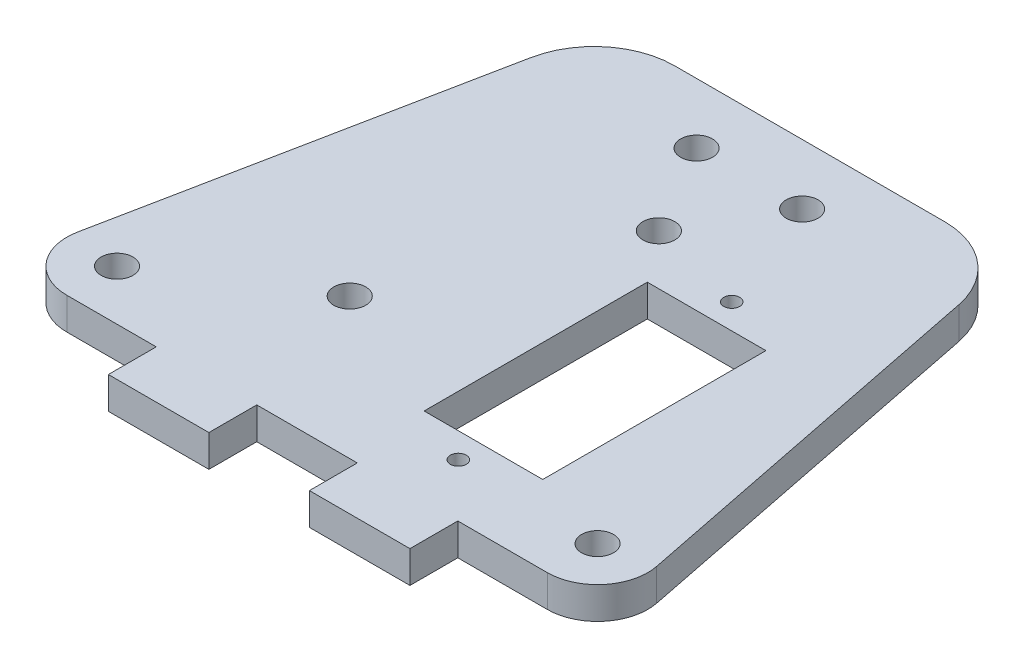
SolidWorks part; units mm, degrees
ref_plane "Alzado" through (0, 0, 0) normal (0, 0, 1) x (1, 0, 0)
ref_plane "Planta" through (0, 0, 0) normal (0, 1, 0) x (1, 0, 0)
ref_plane "Vista lateral" through (0, 0, 0) normal (1, 0, 0) x (0, 0, -1)
sketch "Croquis1" plane through (0, 0, 0) normal (0, 1, 0) x (1, 0, 0)
  line L0 (8.7138, 43.5689) -> (0, 0)
  line L1 (16.5584, 50) -> (43.4416, 50)
  line L3 (0, 0) -> (60, 0)
  line L5 (51.2862, 43.5689) -> (60, 0)
  line L6 (33.85, 7.8) -> (45.65, 2.8) construction
  line L7 (33.85, 30) -> (45.65, 30)
  line L9 (33.85, 30) -> (33.85, 7.8)
  line L10 (33.85, 7.8) -> (45.65, 7.8) construction
  line L11 (30, -1000) -> (30, 49000) construction
  line L12 (45.65, 30) -> (45.65, 7.8)
  line L13 (33.85, 30) -> (45.65, 30) construction
  line L14 (33.85, 30) -> (33.85, 35) construction
  line L15 (33.85, 35) -> (45.65, 35) construction
  line L16 (45.65, 30) -> (45.65, 35) construction
  line L17 (45.65, 7.8) -> (33.85, 7.8)
  line L18 (45.65, 7.8) -> (45.65, 2.8) construction
  line L19 (45.65, 2.8) -> (33.85, 2.8) construction
  line L20 (33.85, 7.8) -> (33.85, 2.8) construction
  line L21 (45.65, 2.8) -> (45.65, 35) construction
  line L22 (45.65, 35) -> (33.85, 30) construction
  line L23 (33.85, 35) -> (45.65, 30) construction
  line L24 (33.85, 2.8) -> (45.65, 7.8) construction
  circle A0 centre (20.25, 14) radius 9.5 construction
  circle A1 centre (39.75, 14) radius 9.5 construction
  circle A2 centre (20.25, 14) radius 12.5 construction
  circle A3 centre (39.75, 14) radius 12.5 construction
  circle A4 centre (39.75, 5.3) radius 0.7937
  circle A5 centre (39.75, 32.5) radius 0.7937
  circle A6 centre (20.25, 14) radius 1.5875
  circle A7 centre (24.75, 44) radius 1.5875
  circle A8 centre (35.25, 44) radius 1.5875
  circle A9 centre (24.75, 44) radius 4.7625 construction
  circle A10 centre (35.25, 44) radius 4.7625 construction
  arc A11 (51.2862, 43.5689) -> (43.4416, 50) centre (43.4416, 42) ccw
  arc A12 (8.7138, 43.5689) -> (16.5584, 50) centre (16.5584, 42) cw
  point P7 (50, 50)
  point P15 (30, 0)
  point P38 (10, 50)
  dimension "D6" = 19
  dimension "D7" = 19
  dimension "D5" = 25
  dimension "D10" = 25
  dimension "D18" = 1.5875
  dimension "D19" = 1.5875
  dimension "D20" = 3.175
  dimension "D21" = 3.175
  dimension "D22" = 3.175
  dimension "D26" = 9.525
  dimension "D27" = 9.525
  dimension "D29" = 8
  dimension "D1" = 60
  dimension "D3" = 40
  dimension "D4" = 20
  dimension "D8" = 19.5
  dimension "D9" = 14
  dimension "D11" = 9.75
  dimension "D12" = 22.2
  dimension "D13" = 11.8
  dimension "D14" = 5
  dimension "D15" = 5.9
  dimension "D16" = 5
  dimension "D17" = 7.8
  dimension "D23" = 4.5
  dimension "D24" = 4.5
  dimension "D25" = 30
  dimension "D28" = 50
extrude "Saliente-Extruir1" add sketch "Croquis1" along normal blind 3.175
sketch "Croquis2" plane through (0, 3.175, 0) normal (0, 1, 0) x (1, 0, 0)
  line L0 (0, 0) -> (60, 0) construction
  line L2 (60, 0) -> (51.2862, 43.5689) construction
  line L3 (53.901, 0) -> (60, 0)
  line L7 (43.4416, 50) -> (16.5584, 50)
  line L8 (8.7138, 43.5689) -> (0, 0)
  line L9 (0, 0) -> (60, 0)
  line L10 (60, 0) -> (51.2862, 43.5689)
  line L12 (1.1961, 5.9806) -> (0, 0)
  line L13 (0, 0) -> (6.099, 0)
  line L14 (60, 0) -> (58.8039, 5.9806)
  circle A0 centre (30, 35) radius 1.5875
  circle A1 centre (6.099, 5) radius 1.5875
  circle A2 centre (53.901, 5) radius 1.5875
  circle A3 centre (24.75, 44) radius 4.7625 construction
  circle A4 centre (35.25, 44) radius 4.7625 construction
  arc A6 (53.901, 0) -> (58.8039, 5.9806) centre (53.901, 5) ccw
  arc A7 (1.1961, 5.9806) -> (6.099, 0) centre (6.099, 5) ccw
  arc A9 (51.2862, 43.5689) -> (43.4416, 50) centre (43.4416, 42) ccw
  arc A10 (16.5584, 50) -> (8.7138, 43.5689) centre (16.5584, 42) ccw
  dimension "D1" = 9.525
  dimension "D2" = 9.525
  dimension "D3" = 3.175
  dimension "D4" = 3.175
  dimension "D5" = 3.175
  dimension "D6" = 5
  dimension "D7" = 10
  dimension "D9" = 5
  dimension "D10" = 30
  dimension "D11" = 35
  dimension "D8" = 0
extrude "Cortar-Extruir1" cut sketch "Croquis2" against normal blind 3.175
sketch "Croquis3" plane through (0, 3.175, 0) normal (0, 1, 0) x (1, 0, 0)
  line L0 (6.099, 0) -> (53.901, 0) construction
  line L1 (15, 0) -> (25, 0)
  line L2 (15, 0) -> (15, -4.7625)
  line L3 (15, -4.7625) -> (25, -4.7625)
  line L4 (25, 0) -> (25, -4.7625)
  line L5 (30, -950) -> (30, 49050) construction
  line L6 (35, 0) -> (45, 0)
  line L7 (35, 0) -> (35, -4.7625)
  line L8 (35, -4.7625) -> (45, -4.7625)
  line L9 (45, 0) -> (45, -4.7625)
  line L10 (43.4416, 50) -> (16.5584, 50) construction
  point P15 (30, 50)
  dimension "D1" = 10
  dimension "D2" = 10
  dimension "D3" = 10
  dimension "D4" = 5
  dimension "D5" = 4.7625
extrude "Saliente-Extruir2" add sketch "Croquis3" against normal blind 3.175
